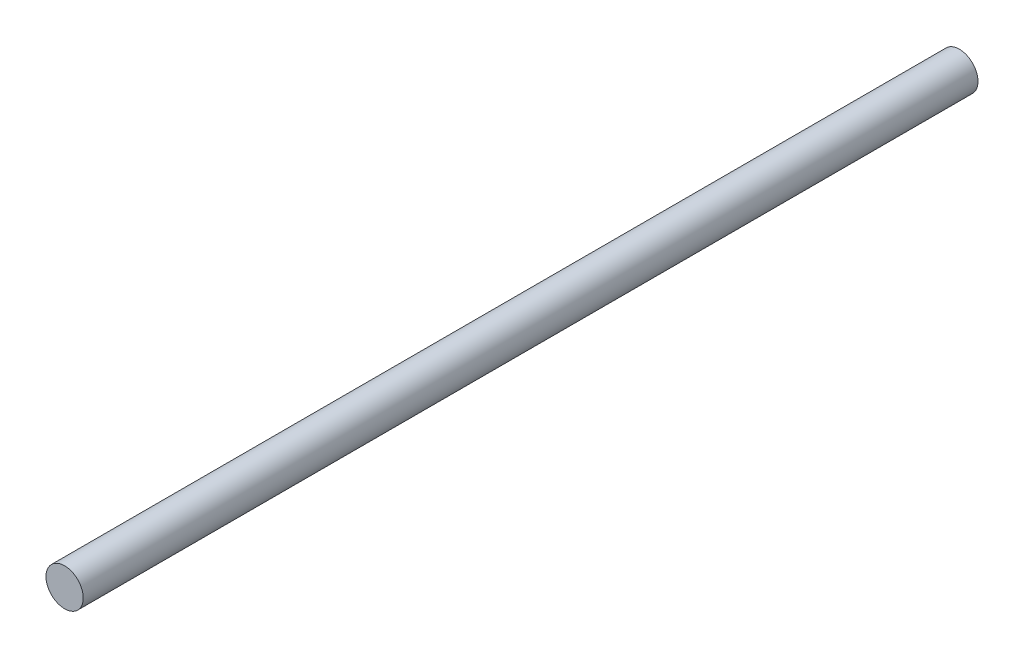
SolidWorks part; units mm, degrees
ref_plane "Front Plane" through (0, 0, 0) normal (0, 0, 1) x (1, 0, 0)
ref_plane "Top Plane" through (0, 0, 0) normal (0, 1, 0) x (1, 0, 0)
ref_plane "Right Plane" through (0, 0, 0) normal (1, 0, 0) x (0, 0, -1)
sketch "Croquis2" plane through (0, 0, 0) normal (0, 0, 1) x (1, 0, 0)
  circle A0 centre (0, 0) radius 2.5
  dimension "D1" = 5
extrude "Saliente-Extruir1" add sketch "Croquis2" along normal blind 120
